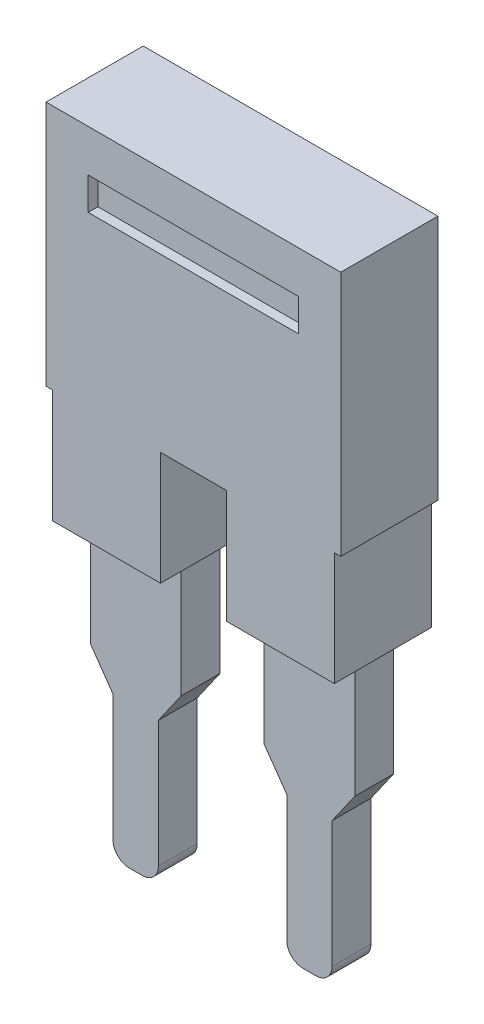
SolidWorks part; units mm, degrees
material "ABS_eSun_GRN"
ref_plane "Front Plane" through (0, 0, 0) normal (0, 0, 1) x (1, 0, 0)
ref_plane "Top Plane" through (0, 0, 0) normal (0, 1, 0) x (1, 0, 0)
ref_plane "Right Plane" through (0, 0, 0) normal (1, 0, 0) x (0, 0, -1)
sketch "Sketch1" plane through (0, 0, 0) normal (0, 0, 1) x (1, 0, 0)
  line L0 (0, 0) -> (0, 17.0262) construction
  line L1 (0, -50) -> (0, 50) construction
  line L2 (0, 7.6) -> (4.55, 7.6)
  line L3 (4.55, 7.6) -> (4.55, 0)
  line L4 (4.55, 0) -> (4.35, 0)
  line L5 (4.35, 0) -> (4.35, -3.5)
  line L6 (4.35, -3.5) -> (1.015, -3.5)
  line L7 (1.015, -3.5) -> (1.015, 0)
  line L8 (0, 0) -> (1000, 0) construction
  line L9 (1.015, 0) -> (0, 0)
  line L10 (0, 0) -> (0, 7.6)
  dimension "D1" = 9.1
  dimension "D2" = 8.7
  dimension "D3" = 2.03
  dimension "D4" = 3.5
  dimension "D5" = 7.6
extrude "plastic body" add sketch "Sketch1" along normal mid plane 3
mirror "Mirror1" about plane through (0, 0, 0) normal (1, 0, 0) of "plastic body"
sketch "Sketch2" plane through (0, 0, 1.5) normal (0, 0, 1) x (1, 0, 0)
  line L0 (4.55, 7.6) -> (-4.55, 7.6) construction
  line L1 (-3.25, 6.3) -> (3.25, 6.3)
  line L2 (-3.25, 6.3) -> (-3.25, 5.3)
  line L3 (-3.25, 5.3) -> (3.25, 5.3)
  line L4 (3.25, 6.3) -> (3.25, 5.3)
  point P4 (0, 5.3)
  dimension "D1" = 1.3
  dimension "D2" = 1
  dimension "D3" = 6.5
extrude "cut grip" cut sketch "Sketch2" against normal mid plane 0.6
mirror "Mirror2" about plane through (0, 0, 0) normal (0, 0, 1) of "cut grip"
sketch "sketch_boundary" plane through (0, 0, 0) normal (1, 0, 0) x (0, 0, -1)
  line L0 (-0.6, -3.5) -> (0.6, -3.5) construction
  line L1 (-1.5, -3.5) -> (1.5, -3.5) construction
  line L2 (0.6, -3.5) -> (0.95, -8) construction
  line L3 (0.95, -8) -> (0.6, -12.5) construction
  line L4 (0.6, -12.5) -> (-0.6, -12.5) construction
  line L5 (-0.6, -12.5) -> (-0.95, -8) construction
  line L6 (-0.95, -8) -> (-0.6, -3.5) construction
  arc A0 (-0.6, -3.5) -> (-0.6, -12.5) centre (28.1536, -8) ccw
  point P8 (-0.95, -8)
  point P9 (0, -3.5)
  point P11 (0, -12.5)
  dimension "D1" = 9
  dimension "D2" = 1.2
  dimension "D3" = 1.9
sketch "Sketch4" plane through (0, 0, 0) normal (0, 0, 1) x (1, 0, 0)
  line L0 (1.2825, -3.5) -> (1.2825, -7.1)
  line L1 (1.015, -3.5) -> (4.35, -3.5) construction
  line L2 (1.2825, -7.1) -> (1.9825, -8.1)
  line L3 (1.9825, -8.1) -> (1.9825, -12.5)
  line L4 (1.9825, -12.5) -> (3.3825, -12.5)
  line L5 (3.3825, -12.5) -> (3.3825, -8.1)
  line L6 (3.3825, -8.1) -> (4.0825, -7.1)
  line L7 (4.0825, -7.1) -> (4.0825, -3.5)
  line L8 (4.0825, -3.5) -> (1.2825, -3.5)
  line L9 (1.9825, -8.1) -> (3.3825, -8.1) construction
  point P8 (2.6825, -3.5)
  point P11 (2.6825, -12.5)
  dimension "D1" = 1.4
  dimension "D2" = 2.8
  dimension "D3" = 4.6
  dimension "D4" = 3.6
  dimension "D5" = 9
extrude "Boss-Extrude2" add sketch "Sketch4" along normal mid plane 1.2 separate body
fillet "Fillet1" radius 0.5 2 edges at (1.9825, -12.5, 0) (3.3825, -12.5, 0)
mirror "Mirror4" about plane through (0, 0, 0) normal (1, 0, 0) of "Boss-Extrude2", "Fillet1"
equation "\"thick\"=3"
equation "\"D1@plastic body\" = \"thick\""
